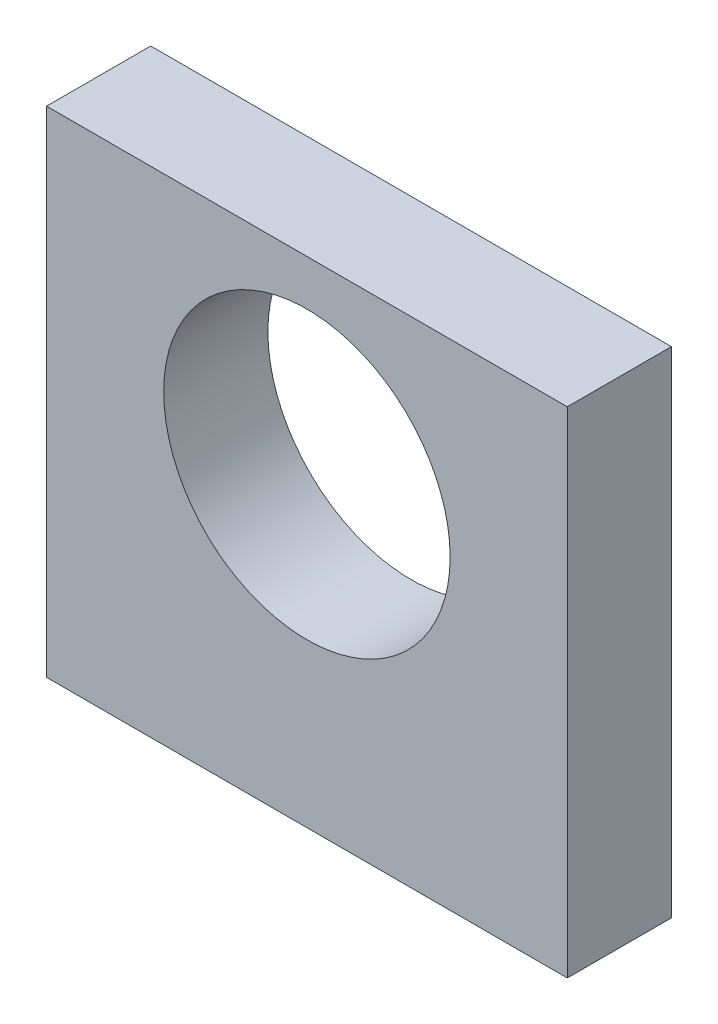
SolidWorks part; units mm, degrees
material "Liga 6061"
ref_plane "Plano frontal" through (0, 0, 0) normal (0, 0, 1) x (1, 0, 0)
ref_plane "Plano superior" through (0, 0, 0) normal (0, 1, 0) x (1, 0, 0)
ref_plane "Plano direito" through (0, 0, 0) normal (1, 0, 0) x (0, 0, -1)
sketch "Esboço1" plane through (0, 0, 0) normal (0, 0, 1) x (1, 0, 0)
  line L1 (20, -19) -> (-20, -19)
  line L2 (20, -19) -> (20, 19)
  line L3 (20, 19) -> (-20, 19)
  line L4 (-20, -19) -> (-20, 19)
  line L5 (20, -19) -> (-20, 19) construction
  line L6 (20, 19) -> (-20, -19) construction
  point P0 (0, 0)
  dimension "D1" = 38
  dimension "D2" = 40
extrude "Ressalto-extrusão1" add sketch "Esboço1" along normal blind 8
sketch "Esboço2" plane through (0, 0, 8) normal (0, 0, 1) x (1, 0, 0)
  line L0 (0, 21.191) -> (0, -23.0958) construction
  line L1 (-20, -19) -> (20, -19) construction
  circle A0 centre (0, 4.5) radius 11
  dimension "D1" = 22
  dimension "D2" = 23.5
extrude "Corte-extrusão1" cut sketch "Esboço2" against normal through all
hole_wizard "Furo roscado para conduíte de M3x0.51" positions "Esboço4" profile "Esboço5" tap size "M3x0.5" standard "Helicoil® Metric"
sketch "Esboço4" plane through (0, -19, 0) normal (0, -1, 0) x (-1, 0, 0)
  line L0 (-20, -8) -> (-20, 0) construction
  line L1 (20, 0) -> (-20, 0) construction
  line L2 (20, -8) -> (20, 0) construction
  point P0 (-12, -4)
  point P2 (12, -4)
  dimension "D1" = 8
  dimension "D2" = 4
  dimension "D3" = 8
  dimension "D4" = 4
sketch "Esboço5" plane through (12, -19, 4) normal (1, 0, 0) x (0, 0, -1)
  line L0 (0, 0) -> (0, 10.9464)
  line L1 (0, 10.9464) -> (1.575, 10)
  line L2 (1.575, 10) -> (1.575, 0.308)
  line L3 (1.575, 0.308) -> (1.883, 0)
  line L5 (1.883, 0) -> (0, 0)
  line L6 (-1.575, 0.308) -> (-1.883, 0) construction
  line L10 (0, 10.9464) -> (-1.575, 10) construction
  line L11 (0, -6.35) -> (0, 107.95) construction
  dimension "Tap Drill Dia." = 3.15
  dimension "Tap Drill Depth" = 10
  dimension "Near C'Sink Dia." = 3.766
  dimension "Near C'Sink Angle" = 90
  dimension "Drill Angle" = 118
cosmetic thread "Rosca de furo1" parameters "D1"=3.5, "D2"=3.716
cosmetic thread "Rosca de furo2" parameters "D1"=3.5, "D2"=3.716
